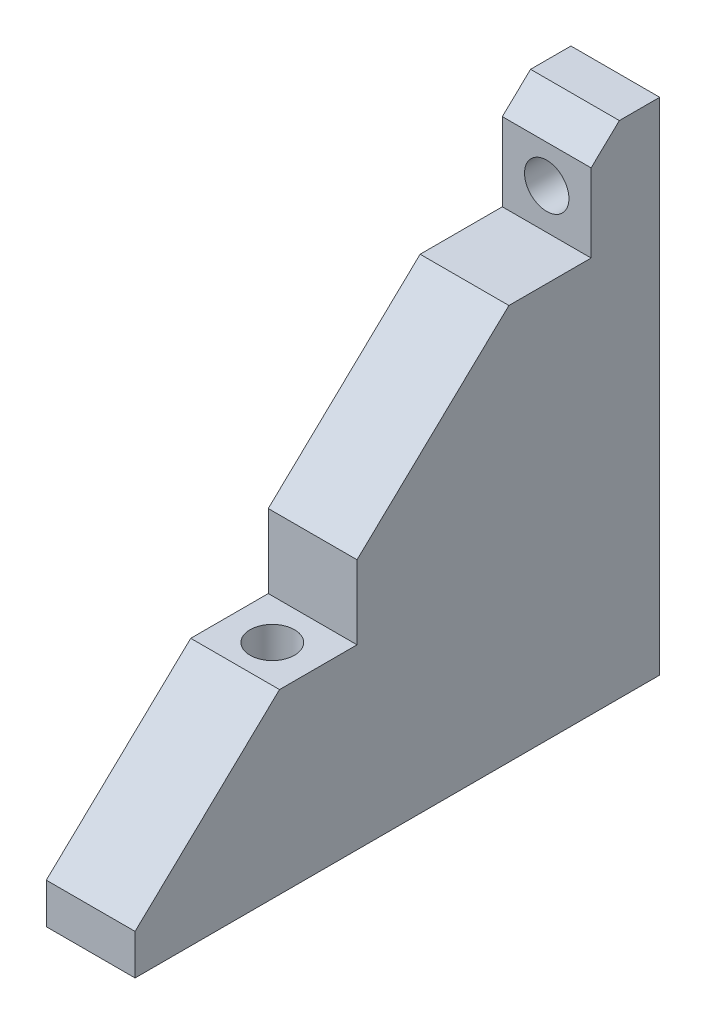
SolidWorks part; units mm, degrees
ref_plane "Front Plane" through (0, 0, 0) normal (0, 0, 1) x (1, 0, 0)
ref_plane "Top Plane" through (0, 0, 0) normal (0, 1, 0) x (1, 0, 0)
ref_plane "Right Plane" through (0, 0, 0) normal (1, 0, 0) x (0, 0, -1)
sketch "Sketch1" plane through (0, 0, 0) normal (0, 0, 1) x (1, 0, 0)
  line L0 (0, 0) -> (0, -161.0316) construction
  line L1 (-32.5, -137) -> (32.5, -137)
  line L2 (-32.5, -137) -> (-32.5, -80)
  line L3 (-32.5, -80) -> (32.5, -80)
  line L4 (32.5, -137) -> (32.5, -80)
  line L5 (0, -100) -> (0, -80) construction
  circle A1 centre (0, 0) radius 100 construction
  point P7 (0, -80)
  dimension "D2" = 20
  dimension "D1" = 10
  dimension "D3" = 65
extrude "Boss-Extrude1" add sketch "Sketch1" against normal blind 5
sketch "Sketch2" plane through (0, -137, 0) normal (0, -1, 0) x (1, 0, 0)
  line L0 (32.5, -5) -> (32.5, 0) construction
  line L1 (-32.5, -5) -> (32.5, -5)
  line L2 (-32.5, -5) -> (-32.5, 60)
  line L3 (-32.5, 60) -> (32.5, 60)
  line L4 (32.5, -5) -> (32.5, 60)
  line L5 (0, 60) -> (0, 0) construction
  line L6 (32.5, 27.5) -> (-32.5, 27.5) construction
  line L7 (21, 47.5) -> (-20, 47.5) construction
  circle A0 centre (20, 37.5) radius 2.75
  circle A1 centre (21, 47.5) radius 5
  circle A4 centre (-20, 47.5) radius 5
  circle A5 centre (-20, 7.5) radius 5
  circle A6 centre (21, 7.5) radius 5
  circle A7 centre (-20, 37.5) radius 2.75
  dimension "D3" = 5.5
  dimension "D6" = 10
  dimension "D9" = 10
  dimension "D1" = 65
  dimension "D2" = 12.5
  dimension "D4" = 22.5
  dimension "D5" = 12.5
  dimension "D7" = 21
  dimension "D8" = 20
extrude "Boss-Extrude2" add sketch "Sketch2" along normal blind 5
sketch "Sketch3" plane through (0, -137, 0) normal (0, 1, 0) x (1, 0, 0)
  line L6 (32.5, 0) -> (-32.5, 0) construction
  line L7 (25.5, 0) -> (14.5, 0)
  line L9 (0, 0) -> (0, -67.5782) construction
  line L14 (25.5, 0) -> (25.5, -60)
  line L15 (25.5, -60) -> (14.5, -60)
  line L16 (14.5, 0) -> (14.5, -60)
  line L17 (32.5, -60) -> (-32.5, -60) construction
  line L18 (20, -37.5) -> (14.5, -37.5) construction
  line L19 (20, -37.5) -> (25.5, -37.5) construction
  line L20 (-25.5, 0) -> (-14.5, 0)
  line L21 (-25.5, 0) -> (-25.5, -60)
  line L22 (-14.5, 0) -> (-14.5, -60)
  line L23 (-25.5, -60) -> (-14.5, -60)
  dimension "D1" = 5.5
extrude "Boss-Extrude7" add sketch "Sketch3" along normal up to surface (57 mm away) up to face at (0, -80, -2.5)
sketch "Sketch5" plane through (25.5, 0, 0) normal (1, 0, 0) x (0, 0, -1)
  line L0 (-60, -137) -> (0, -80)
  line L1 (0, -80) -> (-60, -80)
  line L2 (-60, -80) -> (-60, -137)
extrude "Cut-Extrude2" cut sketch "Sketch5" against normal through all
sketch "Sketch6" plane through (0, -137, 0) normal (0, -1, 0) x (1, 0, 0)
  circle A0 centre (-20, 37.5) radius 2.75 construction
  circle A1 centre (20, 37.5) radius 2.75 construction
  circle A2 centre (-20, 37.5) radius 2.75
  circle A3 centre (20, 37.5) radius 2.75
extrude "Cut-Extrude3" cut sketch "Sketch6" against normal through all
sketch "Sketch7" plane through (0, 0, 60) normal (0, 0, 1) x (1, 0, 0)
  line L0 (-20, -137) -> (-20, -73.184) construction
  line L1 (-25.5, -137) -> (-14.5, -137) construction
  line L2 (0, -142) -> (0, -80) construction
  line L3 (32.5, -142) -> (-32.5, -142) construction
  line L4 (14.5, -80) -> (-14.5, -80) construction
  line L5 (-25.5, -80) -> (-14.5, -80) construction
  circle A1 centre (-20, -88) radius 2.75
  circle A2 centre (20, -88) radius 2.75
  dimension "D1" = 5.5
  dimension "D2" = 8
extrude "Cut-Extrude4" cut sketch "Sketch7" against normal through all
sketch "Sketch8" plane through (0, -137, 0) normal (0, 1, 0) x (1, 0, 0)
  line L0 (25.5, -60) -> (25.5, 0) construction
  line L1 (25.5, -42.5) -> (14.5, -42.5)
  line L2 (25.5, -42.5) -> (25.5, -32.5)
  line L3 (25.5, -32.5) -> (14.5, -32.5)
  line L4 (14.5, -42.5) -> (14.5, -32.5)
  line L5 (14.5, -60) -> (14.5, 0) construction
  line L6 (25.5, -42.5) -> (14.5, -32.5) construction
  line L7 (0, 0) -> (0, -60) construction
  line L8 (14.5, 0) -> (-14.5, 0) construction
  line L9 (14.5, -60) -> (-14.5, -60) construction
  line L10 (-25.5, -42.5) -> (-25.5, -32.5)
  line L11 (-25.5, -32.5) -> (-14.5, -32.5)
  line L12 (-14.5, -42.5) -> (-14.5, -32.5)
  line L13 (-25.5, -42.5) -> (-14.5, -42.5)
  point P8 (20, -37.5)
  dimension "D1" = 10
extrude "Cut-Extrude5" cut sketch "Sketch8" against normal blind 40 from surface at 57 starting at face at (0, -80, -1.25)
sketch "Sketch9" plane through (0, 0, 0) normal (0, 0, 1) x (1, 0, 0)
  line L0 (-14.5, -80) -> (-14.5, -110.875) construction
  line L1 (-14.5, -93) -> (-25.5, -93)
  line L2 (-14.5, -93) -> (-14.5, -83)
  line L3 (-14.5, -83) -> (-25.5, -83)
  line L4 (-25.5, -93) -> (-25.5, -83)
  line L5 (-25.5, -110.875) -> (-25.5, -80) construction
  line L6 (0, -137) -> (0, -80) construction
  line L7 (14.5, -137) -> (-14.5, -137) construction
  line L8 (14.5, -80) -> (-14.5, -80) construction
  line L9 (-25.5, -93) -> (-14.5, -83) construction
  line L10 (25.5, -93) -> (25.5, -83)
  line L11 (14.5, -93) -> (25.5, -93)
  line L12 (14.5, -83) -> (25.5, -83)
  line L13 (14.5, -93) -> (14.5, -83)
  point P14 (-20, -88)
  point P17 (-20, -88)
  dimension "D1" = 10
extrude "Cut-Extrude6" cut sketch "Sketch9" against normal blind 56.5 from surface at 60 starting at face at (0, -138.25, 60)
sketch "Sketch10" plane through (0, 0, 60) normal (0, 0, 1) x (1, 0, 0)
  line L0 (32.5, -142) -> (-32.5, -142) construction
  line L1 (-32.5, -80) -> (-25.5, -80)
  line L2 (-32.5, -80) -> (-32.5, -142)
  line L3 (-32.5, -142) -> (-25.5, -142)
  line L4 (-25.5, -80) -> (-25.5, -142)
  line L5 (25.5, -137) -> (25.5, -120) construction
  line L6 (-14.5, -80) -> (14.5, -80)
  line L7 (-14.5, -80) -> (-14.5, -142)
  line L8 (-14.5, -142) -> (14.5, -142)
  line L9 (14.5, -80) -> (14.5, -142)
  line L10 (32.5, -80) -> (25.5, -80)
  line L11 (32.5, -80) -> (32.5, -142)
  line L12 (32.5, -142) -> (25.5, -142)
  line L13 (25.5, -80) -> (25.5, -142)
  line L15 (-25.5, -137) -> (-25.5, -120) construction
  line L16 (14.5, -137) -> (14.5, -120) construction
extrude "Cut-Extrude7" cut sketch "Sketch10" against normal through all
delete or keep bodies "Body-Delete/Keep 1" type keep bodies bodies 111
